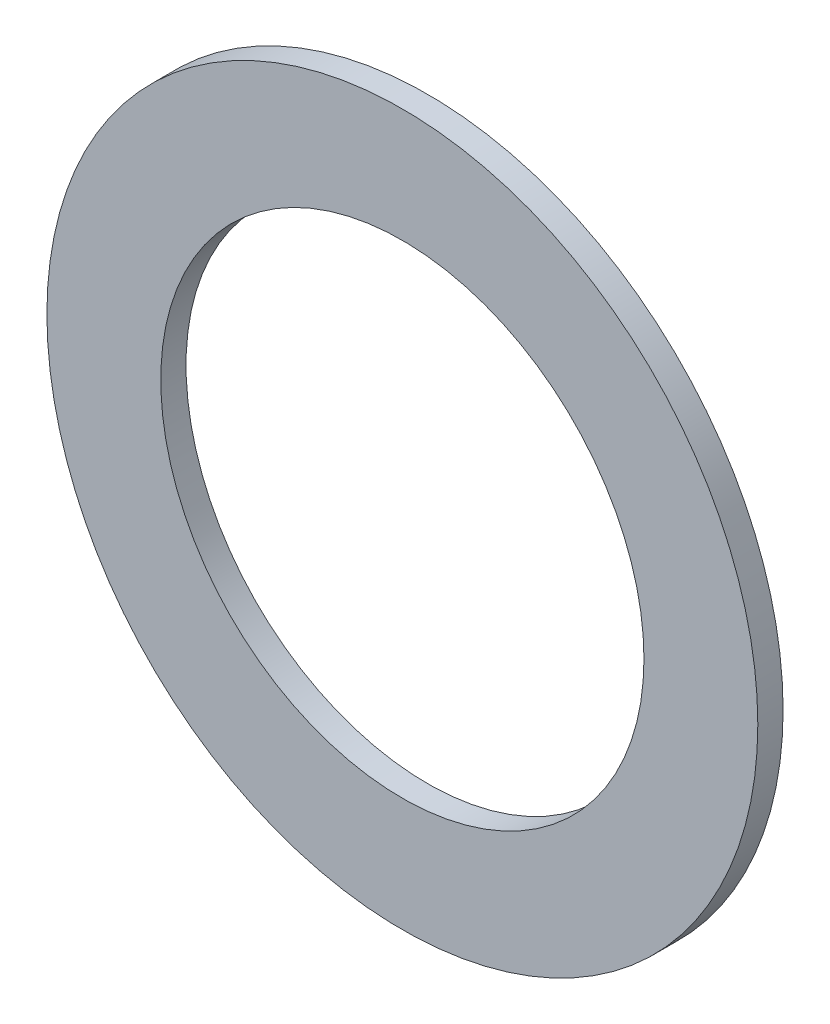
SolidWorks part; units mm, degrees
material "Bismuth"
ref_plane "Front" through (0, 0, 0) normal (0, 0, 1) x (1, 0, 0)
ref_plane "Top" through (0, 0, 0) normal (0, 1, 0) x (1, 0, 0)
ref_plane "Right" through (0, 0, 0) normal (1, 0, 0) x (0, 0, -1)
sketch "Sketch1" plane through (0, 0, 0) normal (0, 0, 1) x (1, 0, 0)
  circle A0 centre (0, 0) radius 128
  circle A1 centre (0, 0) radius 87
extrude "Boss-Extrude2" add sketch "Sketch1" along normal blind 9.1 separate body contours A0 | A1
